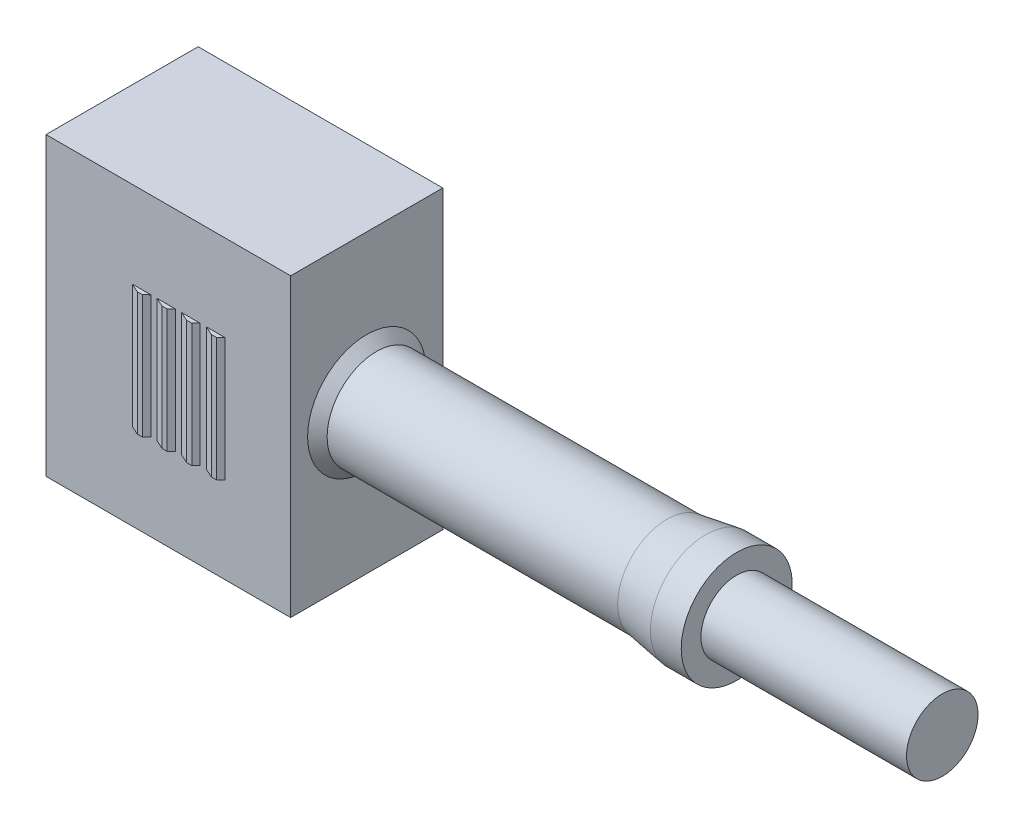
SolidWorks part; units mm, degrees
ref_plane "Front" through (0, 0, 0) normal (0, 0, 1) x (1, 0, 0)
ref_plane "Top" through (0, 0, 0) normal (0, 1, 0) x (1, 0, 0)
ref_plane "Right" through (0, 0, 0) normal (1, 0, 0) x (0, 0, -1)
sketch "Sketch1" plane through (0, 0, 0) normal (0, 0, 1) x (1, 0, 0)
  line L1 (5.95, -7.2) -> (-5.95, -7.2)
  line L2 (5.95, -7.2) -> (5.95, 7.2)
  line L3 (5.95, 7.2) -> (-5.95, 7.2)
  line L4 (-5.95, -7.2) -> (-5.95, 7.2)
  line L5 (5.95, -7.2) -> (-5.95, 7.2) construction
  line L6 (5.95, 7.2) -> (-5.95, -7.2) construction
  point P0 (0, 0)
  dimension "D1" = 11.9
  dimension "D2" = 14.4
extrude "Extrude1" add sketch "Sketch1" along normal mid plane 7.4
sketch "Sketch2" plane through (0, 0, 0) normal (0, 0, 1) x (1, 0, 0)
  line L0 (0, 0) -> (26.7762, 0) construction
  line L1 (5.95, 0) -> (5.95, 2.875)
  line L3 (5.95, -7.2) -> (5.95, 7.2) construction
  line L4 (5.95, 2.875) -> (6.425, 2.4)
  line L5 (6.425, 2.4) -> (20.5559, 2.4)
  line L6 (20.5559, 2.4) -> (22.45, 2.7)
  line L7 (22.45, 2.7) -> (23.95, 2.7)
  line L8 (23.95, 2.7) -> (23.95, 1.74)
  line L9 (23.95, 1.74) -> (33.95, 1.74)
  line L10 (33.95, 1.74) -> (33.95, 0)
  line L11 (33.95, 0) -> (5.95, 0)
  dimension "D1" = 4.8
  dimension "D2" = 5.4
  dimension "D3" = 3.48
  dimension "D4" = 10
  dimension "D5" = 171
  dimension "D6" = 45
  dimension "D7" = 5.75
  dimension "D8" = 18
  dimension "D9" = 1.5
revolve "Revolve1" add sketch "Sketch2" angle 360 about L0
sketch "Sketch3" plane through (0, 0, 0) normal (0, 1, 0) x (1, 0, 0)
  line L0 (-1.75, -3.7) -> (-1.31, -3.9)
  line L1 (5.95, -3.7) -> (-5.95, -3.7) construction
  line L2 (-1.31, -3.9) -> (-1.06, -3.9)
  line L3 (-1.06, -3.9) -> (-0.85, -3.7)
  line L4 (-5.95, -3.7) -> (-5.95, 3.7) construction
  line L5 (-1.75, -3.7) -> (-0.85, -3.7)
  line L6 (-0.55, -3.7) -> (0.35, -3.7)
  line L7 (-0.55, -3.7) -> (-0.11, -3.9)
  line L8 (0.14, -3.9) -> (0.35, -3.7)
  line L9 (-0.11, -3.9) -> (0.14, -3.9)
  line L10 (0.65, -3.7) -> (1.55, -3.7)
  line L11 (0.65, -3.7) -> (1.09, -3.9)
  line L12 (1.34, -3.9) -> (1.55, -3.7)
  line L13 (1.09, -3.9) -> (1.34, -3.9)
  line L14 (1.85, -3.7) -> (2.75, -3.7)
  line L15 (1.85, -3.7) -> (2.29, -3.9)
  line L16 (2.54, -3.9) -> (2.75, -3.7)
  line L17 (2.29, -3.9) -> (2.54, -3.9)
  line L18 (-1.75, -3.7) -> (-0.55, -3.7) construction
  dimension "D1" = 0.2
  dimension "D2" = 4.2
  dimension "D3" = 0.44
  dimension "D4" = 0.25
  dimension "D5" = 0.9
  dimension "D6" = 1.2
extrude "Extrude2" add sketch "Sketch3" along normal mid plane 6
sketch "Sketch4" plane through (-5.95, 0, 0) normal (-1, 0, 0) x (0, 0, 1)
  line L1 (2.8, -6.4) -> (-2.8, -6.4)
  line L2 (2.8, -6.4) -> (2.8, 6.4)
  line L3 (2.8, 6.4) -> (-2.8, 6.4)
  line L4 (-2.8, -6.4) -> (-2.8, 6.4)
  line L5 (2.8, -6.4) -> (-2.8, 6.4) construction
  line L6 (2.8, 6.4) -> (-2.8, -6.4) construction
  point P0 (0, 0)
  dimension "D1" = 12.8
  dimension "D2" = 5.6
extrude "Extrude3" cut sketch "Sketch4" against normal blind 4.5
